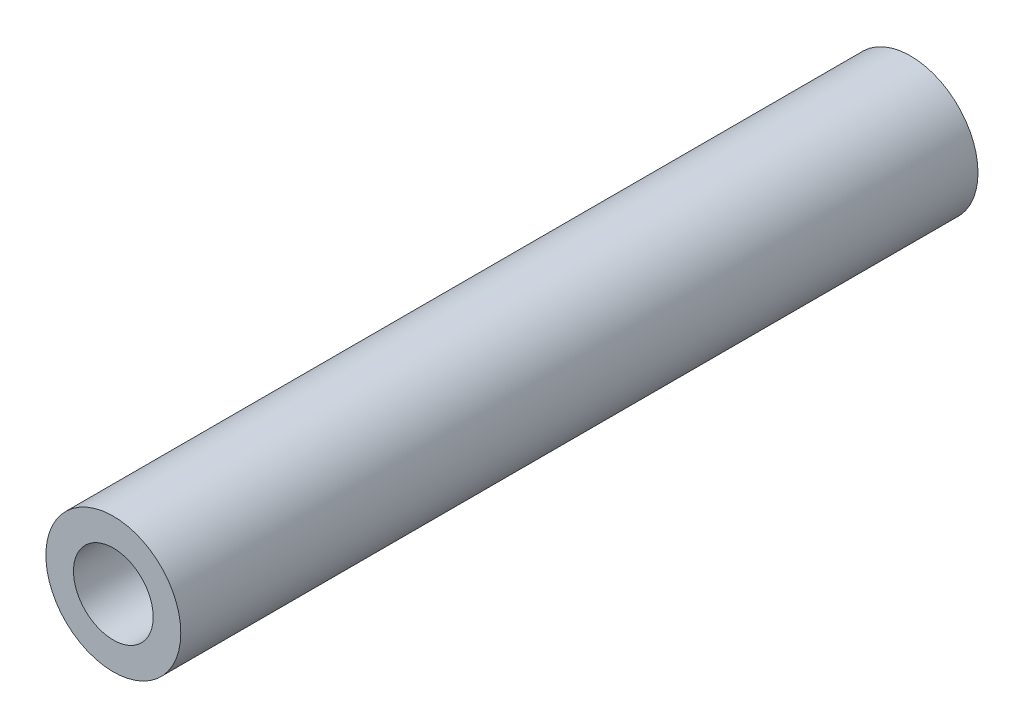
SolidWorks part; units mm, degrees
material "PVC Rígido"
ref_plane "Alzado" through (0, 0, 0) normal (0, 0, 1) x (1, 0, 0)
ref_plane "Planta" through (0, 0, 0) normal (0, 1, 0) x (1, 0, 0)
ref_plane "Vista lateral" through (0, 0, 0) normal (1, 0, 0) x (0, 0, -1)
sketch "Croquis2" plane through (0, 0, 0) normal (0, 0, 1) x (1, 0, 0)
  circle A0 centre (0, 0) radius 6.5
  circle A1 centre (0, 0) radius 11
  dimension "D1" = 13
  dimension "D2" = 22
extrude "Saliente-Extruir1" add sketch "Croquis2" along normal blind 130
